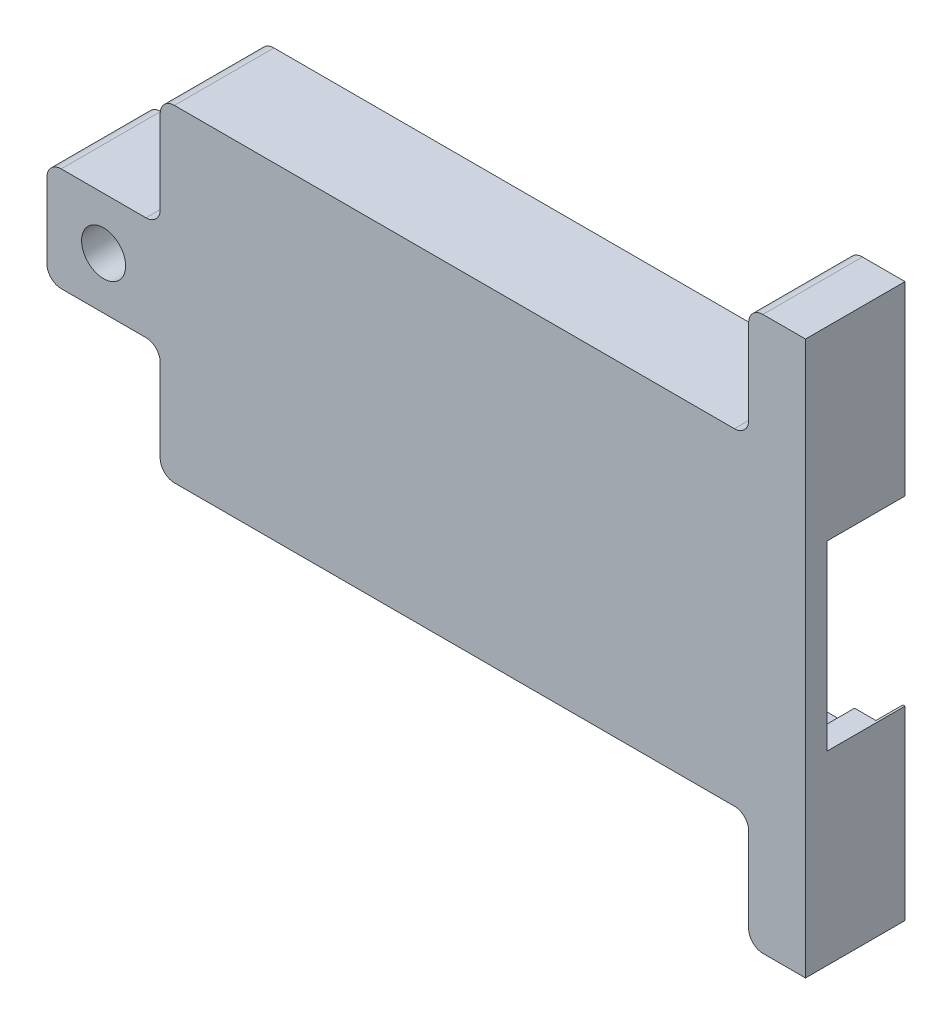
SolidWorks part; units mm, degrees
ref_plane "Alzado" through (0, 0, 0) normal (0, 0, 1) x (1, 0, 0)
ref_plane "Planta" through (0, 0, 0) normal (0, 1, 0) x (1, 0, 0)
ref_plane "Vista lateral" through (0, 0, 0) normal (1, 0, 0) x (0, 0, -1)
sketch "Croquis1" plane through (0, 0, 0) normal (0, 0, 1) x (1, 0, 0)
  line L32 (19.5, 6.4) -> (21.15, 6.4)
  line L33 (21.15, 6.4) -> (21.15, 19.4652)
  line L34 (16.15, 11.5) -> (-23.25, 11.5)
  line L35 (16.15, 11.5) -> (-23.25, 11.5)
  line L36 (-25.25, 3.65) -> (-31.2152, 3.65)
  line L37 (-25.25, 3.65) -> (-31.2152, 3.65)
  line L38 (-32.2152, 2.65) -> (-32.2152, -2.65)
  line L39 (-32.2152, 2.65) -> (-32.2152, -2.65)
  line L40 (-31.2152, -3.65) -> (-25.25, -3.65)
  line L41 (-31.2152, -3.65) -> (-25.25, -3.65)
  line L42 (-24.25, -4.65) -> (-24.25, -10.5)
  line L43 (-24.25, 10.5) -> (-24.25, 4.65)
  line L44 (-24.25, -4.65) -> (-24.25, -10.5)
  line L52 (-23.25, -11.5) -> (16.15, -11.5)
  line L53 (21.15, -19.4652) -> (21.15, -6.4)
  line L54 (21.15, -6.4) -> (19.5, -6.4)
  line L55 (19.5, -6.4) -> (19.5, -9.5)
  line L56 (19.5, -9.5) -> (-19.5, -9.5)
  line L57 (-19.5, -9.5) -> (-19.5, -6.4)
  line L58 (-19.5, -6.4) -> (-22.5, -6.4)
  line L59 (-22.5, -6.4) -> (-22.5, 6.4)
  line L60 (-22.5, 6.4) -> (-19.5, 6.4)
  line L61 (-19.5, 6.4) -> (-19.5, 9.5)
  line L62 (-19.5, 9.5) -> (19.5, 9.5)
  line L63 (19.5, 9.5) -> (19.5, 6.4)
  line L64 (19.5, 6.4) -> (21.15, 6.4)
  line L65 (21.15, 6.4) -> (21.15, 19.4652)
  line L75 (-24.25, 10.5) -> (-24.25, 4.65)
  line L84 (-23.25, -11.5) -> (16.15, -11.5)
  line L85 (21.15, -19.4652) -> (21.15, -6.4)
  line L86 (21.15, -6.4) -> (19.5, -6.4)
  line L87 (19.5, -6.4) -> (19.5, -9.5)
  line L88 (19.5, -9.5) -> (-19.5, -9.5)
  line L89 (-19.5, -9.5) -> (-19.5, -6.4)
  line L90 (-19.5, -6.4) -> (-22.5, -6.4)
  line L91 (-22.5, -6.4) -> (-22.5, 6.4)
  line L92 (-22.5, 6.4) -> (-19.5, 6.4)
  line L93 (-19.5, 6.4) -> (-19.5, 9.5)
  line L94 (-19.5, 9.5) -> (19.5, 9.5)
  line L95 (19.5, 9.5) -> (19.5, 6.4)
  line L125 (17.15, -12.5) -> (17.15, -18.4652)
  line L126 (17.15, -12.5) -> (17.15, -18.4652)
  line L127 (18.15, -19.4652) -> (21.15, -19.4652)
  line L128 (18.15, -19.4652) -> (21.15, -19.4652)
  line L129 (21.15, 19.4652) -> (18.15, 19.4652)
  line L130 (21.15, 19.4652) -> (18.15, 19.4652)
  line L131 (17.15, 18.4652) -> (17.15, 12.5)
  line L132 (17.15, 18.4652) -> (17.15, 12.5)
  circle A16 centre (-28.2326, 0) radius 1.55 construction
  circle A17 centre (-28.2326, 0) radius 1.55
  arc A20 (17.15, -18.4652) -> (18.15, -19.4652) centre (18.15, -18.4652) ccw
  arc A22 (17.15, -18.4652) -> (18.15, -19.4652) centre (18.15, -18.4652) ccw
  arc A24 (18.15, 19.4652) -> (17.15, 18.4652) centre (18.15, 18.4652) ccw
  arc A26 (18.15, 19.4652) -> (17.15, 18.4652) centre (18.15, 18.4652) ccw
  arc A28 (16.15, 11.5) -> (17.15, 12.5) centre (16.15, 12.5) ccw
  arc A30 (16.15, 11.5) -> (17.15, 12.5) centre (16.15, 12.5) ccw
  arc A32 (-23.25, 11.5) -> (-24.25, 10.5) centre (-23.25, 10.5) ccw
  arc A39 (-23.25, 11.5) -> (-24.25, 10.5) centre (-23.25, 10.5) ccw
  arc A63 (-25.25, 3.65) -> (-24.25, 4.65) centre (-25.25, 4.65) ccw
  arc A64 (-25.25, 3.65) -> (-24.25, 4.65) centre (-25.25, 4.65) ccw
  arc A65 (-31.2152, 3.65) -> (-32.2152, 2.65) centre (-31.2152, 2.65) ccw
  arc A66 (-31.2152, 3.65) -> (-32.2152, 2.65) centre (-31.2152, 2.65) ccw
  arc A67 (-32.2152, -2.65) -> (-31.2152, -3.65) centre (-31.2152, -2.65) ccw
  arc A68 (-32.2152, -2.65) -> (-31.2152, -3.65) centre (-31.2152, -2.65) ccw
  arc A69 (-24.25, -4.65) -> (-25.25, -3.65) centre (-25.25, -4.65) ccw
  arc A70 (-24.25, -4.65) -> (-25.25, -3.65) centre (-25.25, -4.65) ccw
  arc A71 (-24.25, -10.5) -> (-23.25, -11.5) centre (-23.25, -10.5) ccw
  arc A72 (-24.25, -10.5) -> (-23.25, -11.5) centre (-23.25, -10.5) ccw
  arc A73 (17.15, -12.5) -> (16.15, -11.5) centre (16.15, -12.5) ccw
  arc A74 (17.15, -12.5) -> (16.15, -11.5) centre (16.15, -12.5) ccw
  dimension "D1" = 0
extrude "Saliente-Extruir1" add sketch "Croquis1" along normal blind 5.5
sketch "Croquis2" plane through (0, 0, 5.5) normal (0, 0, 1) x (1, 0, 0)
  line L0 (21.15, -6.4) -> (21.15, 6.4)
  line L20 (19.5, 9.5) -> (19.5, 6.4)
  line L21 (19.5, 6.4) -> (21.15, 6.4)
  line L22 (21.15, 6.4) -> (21.15, 19.4652)
  line L23 (16.15, 11.5) -> (-23.25, 11.5)
  line L24 (-24.25, 10.5) -> (-24.25, 4.65)
  line L25 (-25.25, 3.65) -> (-31.2152, 3.65)
  line L26 (-32.2152, 2.65) -> (-32.2152, -2.65)
  line L27 (-31.2152, -3.65) -> (-25.25, -3.65)
  line L28 (-24.25, -4.65) -> (-24.25, -10.5)
  line L29 (-23.25, -11.5) -> (16.15, -11.5)
  line L30 (21.15, -19.4652) -> (21.15, -6.4)
  line L31 (21.15, -6.4) -> (19.5, -6.4)
  line L32 (19.5, -6.4) -> (19.5, -9.5)
  line L33 (19.5, -9.5) -> (-19.5, -9.5)
  line L34 (-19.5, -9.5) -> (-19.5, -6.4)
  line L35 (-19.5, -6.4) -> (-22.5, -6.4)
  line L36 (-22.5, -6.4) -> (-22.5, 6.4)
  line L37 (-22.5, 6.4) -> (-19.5, 6.4)
  line L38 (-19.5, 6.4) -> (-19.5, 9.5)
  line L39 (-19.5, 9.5) -> (19.5, 9.5)
  line L42 (21.15, 6.4) -> (21.15, 19.4652)
  line L43 (16.15, 11.5) -> (-23.25, 11.5)
  line L44 (-24.25, 10.5) -> (-24.25, 4.65)
  line L45 (-25.25, 3.65) -> (-31.2152, 3.65)
  line L46 (-32.2152, 2.65) -> (-32.2152, -2.65)
  line L47 (-31.2152, -3.65) -> (-25.25, -3.65)
  line L48 (-24.25, -4.65) -> (-24.25, -10.5)
  line L49 (-23.25, -11.5) -> (16.15, -11.5)
  line L50 (21.15, -19.4652) -> (21.15, -6.4)
  line L66 (21.15, 19.4652) -> (18.15, 19.4652)
  line L67 (21.15, 19.4652) -> (18.15, 19.4652)
  line L68 (17.15, 18.4652) -> (17.15, 12.5)
  line L69 (17.15, 18.4652) -> (17.15, 12.5)
  line L70 (17.15, -12.5) -> (17.15, -18.4652)
  line L71 (17.15, -12.5) -> (17.15, -18.4652)
  line L72 (18.15, -19.4652) -> (21.15, -19.4652)
  line L73 (18.15, -19.4652) -> (21.15, -19.4652)
  circle A0 centre (-28.2326, 0) radius 1.55 construction
  circle A1 centre (-28.2326, 0) radius 1.55
  arc A8 (18.15, 19.4652) -> (17.15, 18.4652) centre (18.15, 18.4652) ccw
  arc A9 (-23.25, 11.5) -> (-24.25, 10.5) centre (-23.25, 10.5) ccw
  arc A10 (-25.25, 3.65) -> (-24.25, 4.65) centre (-25.25, 4.65) ccw
  arc A11 (-31.2152, 3.65) -> (-32.2152, 2.65) centre (-31.2152, 2.65) ccw
  arc A12 (-32.2152, -2.65) -> (-31.2152, -3.65) centre (-31.2152, -2.65) ccw
  arc A13 (-24.25, -4.65) -> (-25.25, -3.65) centre (-25.25, -4.65) ccw
  arc A14 (-24.25, -10.5) -> (-23.25, -11.5) centre (-23.25, -10.5) ccw
  arc A15 (18.15, 19.4652) -> (17.15, 18.4652) centre (18.15, 18.4652) ccw
  arc A17 (-23.25, 11.5) -> (-24.25, 10.5) centre (-23.25, 10.5) ccw
  arc A18 (-25.25, 3.65) -> (-24.25, 4.65) centre (-25.25, 4.65) ccw
  arc A19 (-31.2152, 3.65) -> (-32.2152, 2.65) centre (-31.2152, 2.65) ccw
  arc A20 (-32.2152, -2.65) -> (-31.2152, -3.65) centre (-31.2152, -2.65) ccw
  arc A21 (-24.25, -4.65) -> (-25.25, -3.65) centre (-25.25, -4.65) ccw
  arc A22 (-24.25, -10.5) -> (-23.25, -11.5) centre (-23.25, -10.5) ccw
  arc A28 (16.15, 11.5) -> (17.15, 12.5) centre (16.15, 12.5) ccw
  arc A29 (16.15, 11.5) -> (17.15, 12.5) centre (16.15, 12.5) ccw
  arc A30 (17.15, -12.5) -> (16.15, -11.5) centre (16.15, -12.5) ccw
  arc A31 (17.15, -12.5) -> (16.15, -11.5) centre (16.15, -12.5) ccw
  arc A32 (17.15, -18.4652) -> (18.15, -19.4652) centre (18.15, -18.4652) ccw
  arc A33 (17.15, -18.4652) -> (18.15, -19.4652) centre (18.15, -18.4652) ccw
  dimension "D1" = 0
extrude "Saliente-Extruir2" add sketch "Croquis2" along normal blind 1.5
sketch "Croquis3" plane through (0, 0, 0) normal (0, 0, -1) x (-1, 0, 0)
  line L0 (0, 0) -> (22.5, 0) construction
  line L1 (-21, -9.5) -> (22.5, -9.5)
  line L2 (-21, -9.5) -> (-21, 9.5)
  line L3 (-21, 9.5) -> (22.5, 9.5)
  line L4 (22.5, -9.5) -> (22.5, 9.5)
  line L5 (22.5, -6.4) -> (22.5, 6.4) construction
  line L6 (19.5, 9.5) -> (-19.5, 9.5) construction
  dimension "D2" = 43.5
extrude "Cortar-Extruir1" cut sketch "Croquis3" against normal blind 1.9
sketch "Croquis4" plane through (0, 0, 0) normal (0, 0, -1) x (-1, 0, 0)
  line L0 (3.85, 0) -> (-3.85, 0) construction
  circle A0 centre (-19.15, -14.9652) radius 1.5
  circle A1 centre (-19.15, 14.9652) radius 1.5
  dimension "D1" = 3
extrude "Cortar-Extruir2" cut sketch "Croquis4" against normal blind 3
chamfer "Chaflán1" distance 0.4 angle 45 2 edges at (17.65, -14.9652, 0) (20.65, 14.9652, 0)
